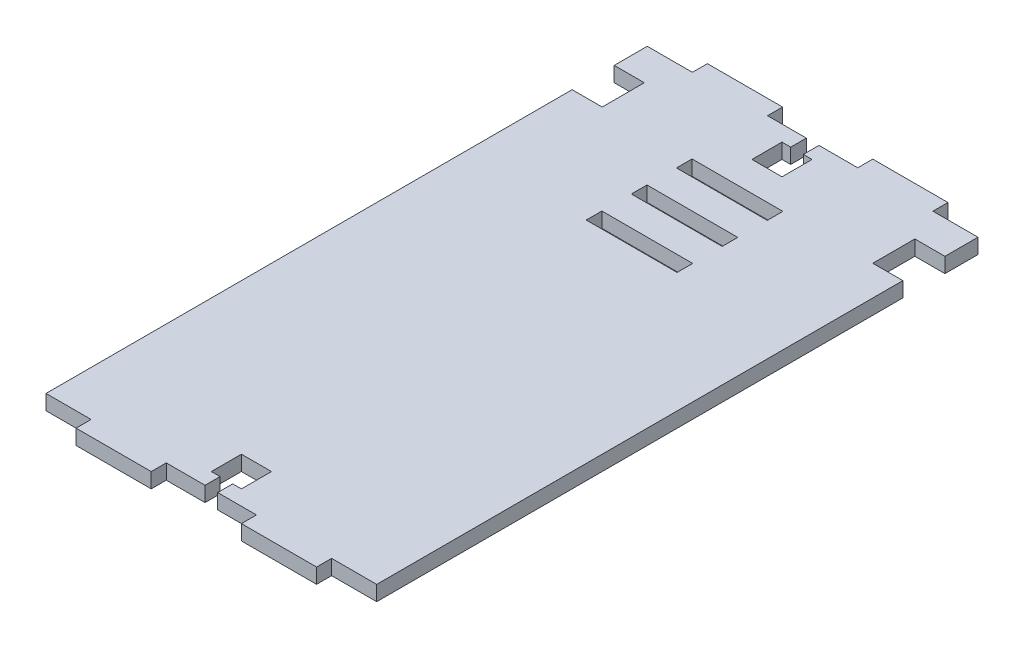
SolidWorks part; units mm, degrees
ref_plane "Front Plane" through (0, 0, 0) normal (0, 0, 1) x (1, 0, 0)
ref_plane "Top Plane" through (0, 0, 0) normal (0, 1, 0) x (1, 0, 0)
ref_plane "Right Plane" through (0, 0, 0) normal (1, 0, 0) x (0, 0, -1)
sketch "Sketch1" plane through (0, 0, 0) normal (0, 0, 1) x (1, 0, 0)
  line L1 (0, 0) -> (-110, 0)
  line L2 (0, 0) -> (0, 5)
  line L3 (0, 5) -> (-110, 5)
  line L4 (-110, 0) -> (-110, 5)
  dimension "D1" = 5
  dimension "D2" = 110
extrude "Boss-Extrude1" add sketch "Sketch1" along normal blind 200
sketch "Sketch2" plane through (0, 5, 0) normal (0, 1, 0) x (1, 0, 0)
  line L0 (0, 0) -> (-110, 0) construction
  line L1 (-95, 0) -> (-70, 0)
  line L2 (-95, 0) -> (-95, 5)
  line L3 (-95, 5) -> (-70, 5)
  line L4 (-70, 0) -> (-70, 5)
  line L5 (-110, -200) -> (-110, 0) construction
  line L6 (-55, 0) -> (-55, -17.2398) construction
  line L7 (-15, 5) -> (-40, 5)
  line L8 (-40, 0) -> (-40, 5)
  line L9 (-15, 0) -> (-40, 0)
  line L10 (-15, 0) -> (-15, 5)
  line L11 (-110, -100) -> (-89.2586, -100) construction
  line L12 (-15, -200) -> (-15, -205)
  line L13 (-15, -200) -> (-40, -200)
  line L14 (-40, -200) -> (-40, -205)
  line L15 (-15, -205) -> (-40, -205)
  line L16 (-95, -205) -> (-70, -205)
  line L17 (-70, -200) -> (-70, -205)
  line L18 (-95, -200) -> (-70, -200)
  line L19 (-95, -200) -> (-95, -205)
  dimension "D1" = 5
  dimension "D2" = 25
  dimension "D3" = 15
extrude "Boss-Extrude2" add sketch "Sketch2" against normal blind 5
sketch "Sketch4" plane through (0, 5, 0) normal (0, 1, 0) x (1, 0, 0)
  line L5 (-70.1, -25) -> (-70.1, -30.2)
  line L6 (-70.1, -25) -> (-39.9, -25)
  line L7 (-39.9, -25) -> (-39.9, -30.2)
  line L8 (-70.1, -30.2) -> (-39.9, -30.2)
  line L9 (-70.1, -40) -> (-70.1, -45.2)
  line L10 (-70.1, -40) -> (-39.9, -40)
  line L11 (-39.9, -40) -> (-39.9, -45.2)
  line L12 (-70.1, -45.2) -> (-39.9, -45.2)
  line L13 (-70.1, -55) -> (-70.1, -60.2)
  line L14 (-70.1, -55) -> (-39.9, -55)
  line L15 (-39.9, -55) -> (-39.9, -60.2)
  line L16 (-70.1, -60.2) -> (-39.9, -60.2)
  line L17 (-70.1, -70) -> (-70.1, -75.2) construction
  line L18 (-70.1, -70) -> (-39.9, -70) construction
  line L19 (-39.9, -70) -> (-39.9, -75.2) construction
  line L20 (-70.1, -75.2) -> (-39.9, -75.2) construction
  line L21 (-70.1, -85) -> (-70.1, -90.2) construction
  line L22 (-70.1, -85) -> (-39.9, -85) construction
  line L23 (-39.9, -85) -> (-39.9, -90.2) construction
  line L24 (-70.1, -90.2) -> (-39.9, -90.2) construction
  line L25 (-70.1, -100) -> (-70.1, -105.2) construction
  line L26 (-70.1, -100) -> (-39.9, -100) construction
  line L27 (-39.9, -100) -> (-39.9, -105.2) construction
  line L28 (-70.1, -105.2) -> (-39.9, -105.2) construction
  line L29 (-70.1, -115) -> (-70.1, -120.2) construction
  line L30 (-70.1, -115) -> (-39.9, -115) construction
  line L31 (-39.9, -115) -> (-39.9, -120.2) construction
  line L32 (-70.1, -120.2) -> (-39.9, -120.2) construction
  line L33 (-70.1, -130) -> (-70.1, -135.2) construction
  line L34 (-70.1, -135.2) -> (-39.9, -135.2) construction
  line L35 (-39.9, -130) -> (-39.9, -135.2) construction
  line L36 (-70.1, -130) -> (-39.9, -130) construction
  line L37 (-70.1, -145) -> (-70.1, -150.2) construction
  line L38 (-70.1, -150.2) -> (-39.9, -150.2) construction
  line L39 (-39.9, -145) -> (-39.9, -150.2) construction
  line L40 (-70.1, -145) -> (-39.9, -145) construction
  line L41 (-110, -200) -> (-110, 0) construction
  dimension "D1" = 39.9
  dimension "D2" = 70.1
  dimension "D3" = 25
  dimension "D4" = 30.2
  dimension "D6" = 40
  dimension "D7" = 55
  dimension "D8" = 70
  dimension "D9" = 85
  dimension "D10" = 100
  dimension "D11" = 115
  dimension "D18" = 130
  dimension "D5" = 3
extrude "Cut-Extrude1" cut sketch "Sketch4" against normal blind 5
sketch "Sketch5" plane through (0, 5, 0) normal (0, 1, 0) x (1, 0, 0)
  line L0 (-40, 0) -> (-70, 0) construction
  line L1 (-57.1, 0) -> (-52.9, 0)
  line L2 (-57.1, 0) -> (-57.1, -5.2)
  line L3 (-57.1, -5.2) -> (-52.9, -5.2)
  line L4 (-52.9, 0) -> (-52.9, -5.2)
  line L5 (-55, -200) -> (-55, -189.6173)
  line L6 (-50, -5.2) -> (-60, -5.2)
  line L7 (-50, -5.2) -> (-50, -15.2)
  line L8 (-50, -15.2) -> (-60, -15.2)
  line L9 (-60, -5.2) -> (-60, -15.2)
  line L10 (-40, -200) -> (-70, -200) construction
  line L12 (-57.1, -200) -> (-52.9, -200)
  line L13 (-57.1, -200) -> (-57.1, -195)
  line L14 (-57.1, -195) -> (-52.9, -195)
  line L15 (-52.9, -200) -> (-52.9, -195)
  line L16 (-60, -195) -> (-50, -195)
  line L17 (-60, -195) -> (-60, -185)
  line L18 (-60, -185) -> (-50, -185)
  line L19 (-50, -195) -> (-50, -185)
  point P10 (-55, 0)
  point P11 (-55, 0)
  point P12 (-55, -5.2)
  point P13 (-55, -5.2)
  dimension "D1" = 5.2
  dimension "D2" = 10
  dimension "D3" = 4.2
  dimension "D4" = 10
  dimension "D5" = 10
  dimension "D6" = 5
  dimension "D7" = 10
  dimension "D8" = 5
  dimension "D9" = 4.2
  dimension "D10" = 5
  dimension "D11" = 2.1
extrude "Cut-Extrude2" cut sketch "Sketch5" against normal blind 10
sketch "Sketch6" plane through (0, 5, 0) normal (0, 1, 0) x (1, 0, 0)
  line L0 (-110, -200) -> (-110, 0) construction
  line L1 (-110, -20) -> (-100, -20)
  line L2 (-110, -20) -> (-110, -25)
  line L3 (-110, -25) -> (-100, -25)
  line L4 (-100, -20) -> (-100, -25)
  line L5 (-95, 0) -> (-110, 0) construction
  line L7 (-55, -25) -> (-55, -18.1364) construction
  line L8 (-39.9, -25) -> (-70.1, -25) construction
  line L9 (-10, -20) -> (-10, -25)
  line L10 (0, -25) -> (-10, -25)
  line L11 (0, -20) -> (0, -25)
  line L12 (0, -20) -> (-10, -20)
  dimension "D1" = 20
  dimension "D2" = 5
  dimension "D3" = 10
extrude "Cut-Extrude3" cut sketch "Sketch6" against normal blind 5
sketch "Sketch7" plane through (0, 0, 0) normal (0, -1, 0) x (1, 0, 0)
  line L0 (-55, 13.4) -> (-55, 18.5809) construction
  line L1 (0, 20) -> (-10, 20)
  line L2 (0, 20) -> (0, 11)
  line L3 (0, 11) -> (-10, 11)
  line L4 (-10, 20) -> (-10, 11)
  line L6 (-100, 20) -> (-100, 11)
  line L7 (-110, 11) -> (-100, 11)
  line L8 (-110, 20) -> (-110, 11)
  line L9 (-110, 20) -> (-100, 20)
  dimension "D1" = 9
extrude "Cut-Extrude4" cut sketch "Sketch7" against normal blind 10
